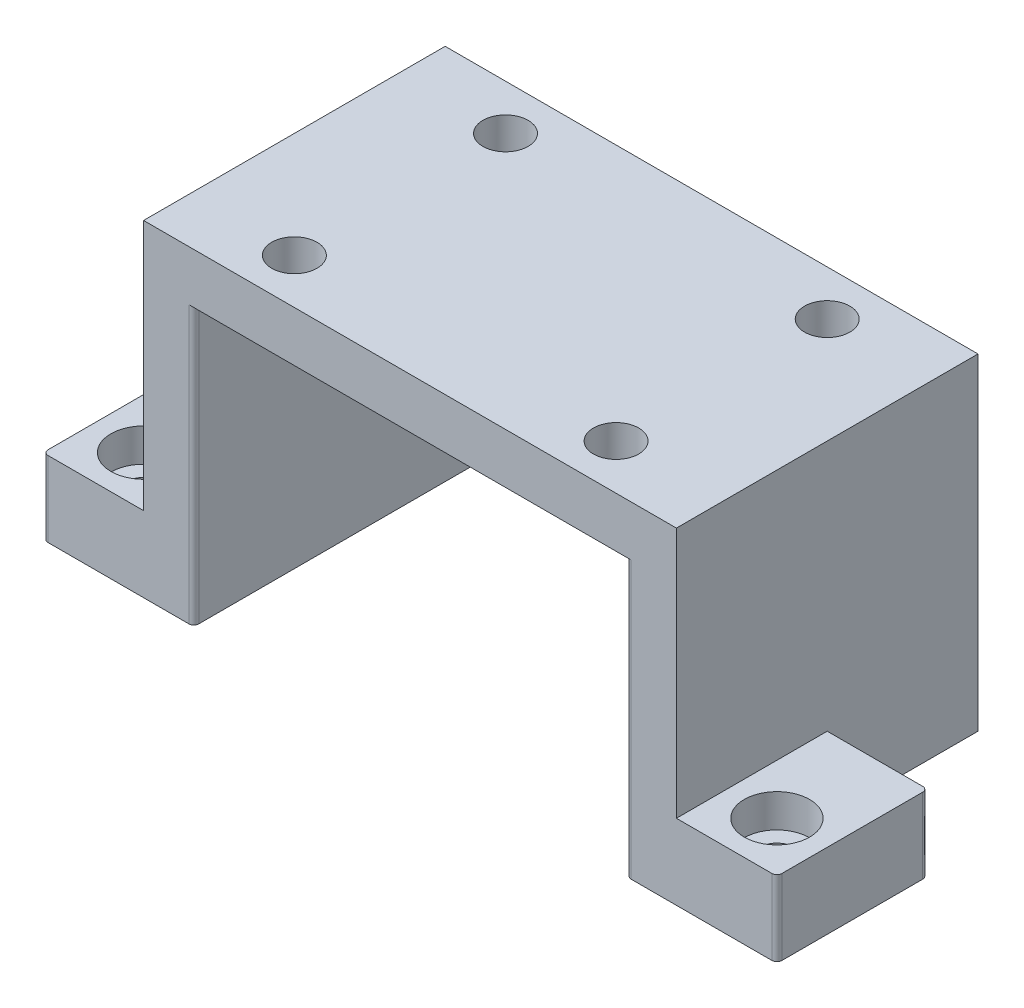
SolidWorks part; units mm, degrees
material "3003 Alloy"
ref_plane "Front Plane" through (0, 0, 0) normal (0, 0, 1) x (1, 0, 0)
ref_plane "Top Plane" through (0, 0, 0) normal (0, 1, 0) x (1, 0, 0)
ref_plane "Right Plane" through (0, 0, 0) normal (1, 0, 0) x (0, 0, -1)
sketch "Sketch1" plane through (0, 0, 0) normal (0, 1, 0) x (1, 0, 0)
  line L1 (-53, -30) -> (53, -30)
  line L2 (-53, -30) -> (-53, 30)
  line L3 (-53, 30) -> (53, 30)
  line L4 (53, -30) -> (53, 30)
  line L5 (-53, -30) -> (53, 30) construction
  line L6 (-53, 30) -> (53, -30) construction
  point P0 (0, 0)
  dimension "D1" = 60
  dimension "D2" = 106
extrude "Boss-Extrude1" add sketch "Sketch1" along normal blind 10
sketch "Sketch2" plane through (0, 0, 0) normal (0, -1, 0) x (1, 0, 0)
  line L0 (53, -30) -> (-53, -30) construction
  line L1 (-53, 30) -> (-43, 30)
  line L2 (-53, 30) -> (-53, -30)
  line L3 (-53, -30) -> (-43, -30)
  line L4 (-43, 30) -> (-43, -30)
  line L6 (53, 30) -> (43, 30)
  line L7 (53, 30) -> (53, -30)
  line L8 (53, -30) -> (43, -30)
  line L9 (43, 30) -> (43, -30)
  dimension "D1" = 10
  dimension "D2" = 10
extrude "Boss-Extrude2" add sketch "Sketch2" along normal blind 55
sketch "Sketch3" plane through (53, 0, 0) normal (1, 0, 0) x (0, 0, -1)
  line L1 (-30, -55) -> (0, -55)
  line L2 (-30, -55) -> (-30, -40)
  line L3 (-30, -40) -> (0, -40)
  line L5 (0, -40) -> (0, -55)
  dimension "D1" = 15
  dimension "D2" = 30
extrude "Boss-Extrude3" add sketch "Sketch3" along normal blind 20
sketch "Sketch4" plane through (-53, 0, 0) normal (-1, 0, 0) x (0, 0, 1)
  line L0 (30, 10) -> (30, -55) construction
  line L1 (-30, -55) -> (30, -55)
  line L2 (-30, -55) -> (-30, -40)
  line L3 (-30, -40) -> (30, -40)
  line L4 (30, -55) -> (30, -40)
  dimension "D1" = 15
extrude "Boss-Extrude4" add sketch "Sketch4" along normal blind 20
sketch "Sketch5" plane through (0, 10, 0) normal (0, 1, 0) x (1, 0, 0)
  line L0 (0, 0) -> (0, 30) construction
  line L1 (53, 30) -> (-53, 30) construction
  line L2 (0, 0) -> (18.8591, 0) construction
  circle A0 centre (-32, 21) radius 4.5
  circle A1 centre (32, 21) radius 4.5
  circle A2 centre (32, -21) radius 4.5
  circle A3 centre (-32, -21) radius 4.5
  dimension "D3" = 9
  dimension "D1" = 32
  dimension "D2" = 21
extrude "Cut-Extrude1" cut sketch "Sketch5" against normal through all
sketch "Sketch6" plane through (0, -40, 0) normal (0, 1, 0) x (1, 0, 0)
  line L1 (73, 0) -> (73, -30) construction
  line L2 (73, -30) -> (53, -30) construction
  line L3 (-73, -30) -> (-73, 30) construction
  line L4 (-73, 30) -> (-53, 30) construction
  line L5 (-73, -30) -> (-53, -30) construction
  circle A1 centre (63, -20) radius 6.5
  circle A2 centre (-63, 20) radius 6.5
  circle A3 centre (-63, -20) radius 6.5
  dimension "D9" = 13
  dimension "D10" = 13
  dimension "D12" = 13
  dimension "D3" = 10
  dimension "D4" = 10
  dimension "D5" = 10
  dimension "D6" = 10
  dimension "D7" = 10
  dimension "D8" = 10
extrude "Cut-Extrude2" cut sketch "Sketch6" against normal blind 6.6
sketch "Sketch7" plane through (0, -46.6, 0) normal (0, 1, 0) x (1, 0, 0)
  circle A0 centre (-63, 20) radius 3.3
  circle A1 centre (-63, -20) radius 3.3
  circle A2 centre (63, -20) radius 3.3
  dimension "D1" = 6.6
  dimension "D2" = 6.6
  dimension "D4" = 6.6
extrude "Cut-Extrude3" cut sketch "Sketch7" against normal through all
fillet "Fillet1" radius 1 8 edges at (43, -27.5, 30) (73, -47.5, 0) (73, -47.5, 30) (43, -27.5, -30) (-43, -27.5, -30) (-73, -47.5, -30) (-73, -47.5, 30) (-43, -27.5, 30)
